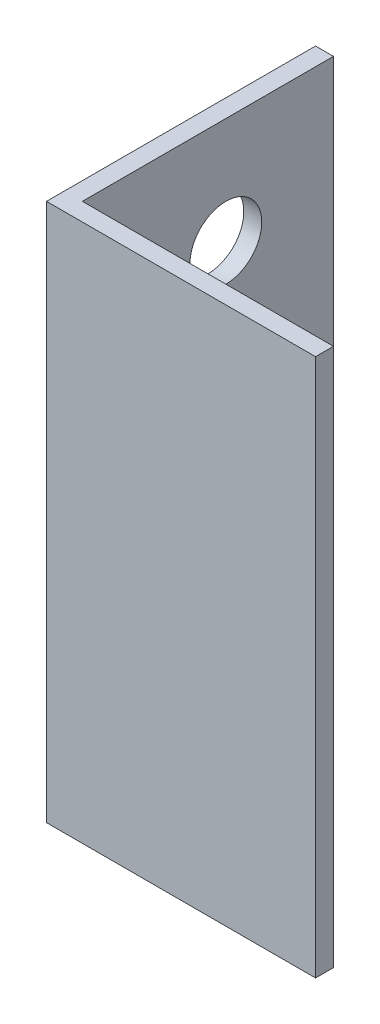
SolidWorks part; units mm, degrees
ref_plane "Спереди" through (0, 0, 0) normal (0, 0, 1) x (1, 0, 0)
ref_plane "Сверху" through (0, 0, 0) normal (0, 1, 0) x (1, 0, 0)
ref_plane "Справа" through (0, 0, 0) normal (1, 0, 0) x (0, 0, -1)
sketch "Эскиз1" plane through (0, 0, 0) normal (0, 1, 0) x (1, 0, 0)
  line L0 (0, 75) -> (0, 0)
  line L1 (0, 0) -> (75, 0)
extrude "Вытянуть-Тонкостенный1" add sketch "Эскиз1" along normal blind 150 thin thin type one direction reverse wall 5
sketch "Эскиз2" plane through (0, 0, 0) normal (-1, 0, 0) x (0, 0, 1)
  line L0 (-75, 150) -> (-75, 0) construction
  line L1 (-75, 150) -> (0, 150) construction
  circle A0 centre (-45, 120) radius 10
  dimension "D1" = 30
  dimension "D2" = 30
extrude "Вырез-Вытянуть1" cut sketch "Эскиз2" against normal through all
